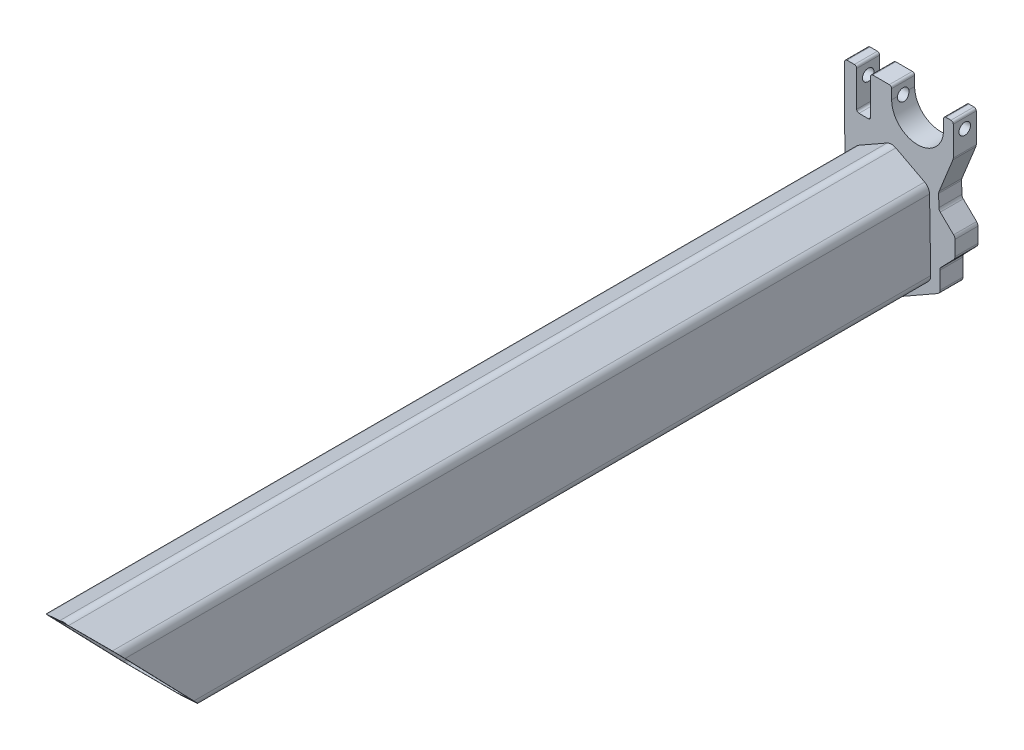
SolidWorks part; units mm, degrees
ref_plane "Front Plane" through (0, 0, 0) normal (0, 0, 1) x (1, 0, 0)
ref_plane "Top Plane" through (0, 0, 0) normal (0, 1, 0) x (1, 0, 0)
ref_plane "Right Plane" through (0, 0, 0) normal (1, 0, 0) x (0, 0, -1)
sketch "Sketch1" plane through (0, 0, 0) normal (0, 0, 1) x (1, 0, 0)
  line L0 (36.798, 101.1427) -> (103.7813, 99.6461) construction
  line L1 (186.6641, 194.1815) -> (187.2024, 162.2454) construction
  line L2 (186.2603, 189.6698) -> (180.1183, 186.1756)
  line L3 (179.6129, 185.2895) -> (179.8695, 170.0721)
  line L4 (180.4044, 169.2036) -> (186.6607, 165.9184)
  line L5 (186.1888, 193.9111) -> (177.0749, 188.7261) construction
  line L6 (176.5695, 187.8401) -> (176.8999, 168.243)
  line L7 (177.4348, 167.3745) -> (186.7183, 162.4997)
  line L8 (193.7621, 169.4288) -> (187.6201, 165.9346)
  line L9 (196.7916, 167.7008) -> (187.6777, 162.5158)
  line L10 (194.0109, 185.5323) -> (194.2674, 170.3148)
  line L11 (196.9666, 188.184) -> (197.297, 168.5868) construction
  line L12 (187.2197, 189.686) -> (193.4759, 186.4008)
  line L13 (187.1482, 193.9273) -> (196.4317, 189.0525) construction
  line L14 (197.297, 168.5868) -> (197.2345, 172.292)
  line L15 (197.5154, 173.004) -> (200.2668, 175.8497)
  line L16 (200.5479, 176.5448) -> (200.5479, 179.7792)
  line L17 (200.2429, 180.4982) -> (197.3418, 183.3031)
  line L18 (197.0371, 184.0052) -> (196.9923, 186.6585)
  line L19 (197.0653, 187.0506) -> (200.0964, 194.5373)
  line L20 (200.1695, 194.9125) -> (200.1695, 201.2852)
  line L21 (199.6695, 201.7852) -> (198.5695, 201.7852)
  line L22 (198.0695, 201.2852) -> (198.0695, 199.1852)
  line L23 (182.6695, 201.7852) -> (186.2695, 201.7852)
  line L24 (186.7695, 201.2852) -> (186.7695, 199.1852)
  line L25 (182.1695, 201.2852) -> (182.1695, 193.5852)
  line L26 (181.6695, 193.0852) -> (179.6695, 193.0852)
  line L27 (179.1695, 193.5852) -> (179.1695, 201.2852)
  line L28 (178.6695, 201.7852) -> (177.0695, 201.7852)
  line L29 (176.5695, 201.2852) -> (176.5695, 187.8401)
  line L30 (176.5695, 201.7852) -> (200.1695, 201.7852) construction
  line L31 (198.0695, 199.1852) -> (186.7695, 199.1852) construction
  arc A0 (177.4348, 167.3745) -> (176.8999, 168.243) centre (177.8997, 168.2598) cw construction
  arc A1 (176.5695, 187.8401) -> (177.0749, 188.7261) centre (177.5694, 187.857) cw construction
  arc A2 (196.9666, 188.184) -> (196.4317, 189.0525) centre (195.9667, 188.1671) ccw construction
  arc A3 (194.2674, 170.3148) -> (193.7621, 169.4288) centre (193.2676, 170.2979) cw
  arc A4 (187.6201, 165.9346) -> (186.6607, 165.9184) centre (187.1256, 166.8037) cw
  arc A5 (180.4044, 169.2036) -> (179.8695, 170.0721) centre (180.8693, 170.0889) cw
  arc A6 (194.0109, 185.5323) -> (193.4759, 186.4008) centre (193.011, 185.5154) ccw
  arc A7 (187.1482, 193.9273) -> (186.1888, 193.9111) centre (186.6833, 193.0419) ccw construction
  arc A8 (187.2197, 189.686) -> (186.2603, 189.6698) centre (186.7548, 188.8006) ccw
  arc A9 (196.7916, 167.7008) -> (197.297, 168.5868) centre (196.2971, 168.57) ccw
  arc A10 (196.4317, 189.0525) -> (196.9666, 188.184) centre (195.9667, 188.1671) cw construction
  arc A11 (176.8999, 168.243) -> (177.4348, 167.3745) centre (177.8997, 168.2598) ccw
  arc A12 (177.0749, 188.7261) -> (176.5695, 187.8401) centre (177.5694, 187.857) ccw construction
  arc A13 (179.6129, 185.2895) -> (180.1183, 186.1756) centre (180.6128, 185.3064) cw
  arc A14 (187.6777, 162.5158) -> (186.7183, 162.4997) centre (187.1832, 163.385) cw
  arc A15 (198.0695, 199.1852) -> (186.7695, 199.1852) centre (192.4195, 199.1852) cw
  arc A16 (200.1695, 194.9125) -> (200.0964, 194.5373) centre (199.1695, 194.9125) cw
  arc A17 (197.0653, 187.0506) -> (196.9923, 186.6585) centre (197.9922, 186.6753) ccw
  arc A18 (197.3418, 183.3031) -> (197.0371, 184.0052) centre (198.0369, 184.022) cw
  arc A19 (200.2429, 180.4982) -> (200.5479, 179.7792) centre (199.5479, 179.7792) cw
  arc A20 (197.5154, 173.004) -> (197.2345, 172.292) centre (198.2344, 172.3089) ccw
  arc A21 (200.2668, 175.8497) -> (200.5479, 176.5448) centre (199.5479, 176.5448) ccw
  arc A22 (176.5695, 201.2852) -> (177.0695, 201.7852) centre (177.0695, 201.2852) cw
  arc A23 (178.6695, 201.7852) -> (179.1695, 201.2852) centre (178.6695, 201.2852) cw
  arc A24 (179.1695, 193.5852) -> (179.6695, 193.0852) centre (179.6695, 193.5852) ccw
  arc A25 (181.6695, 193.0852) -> (182.1695, 193.5852) centre (181.6695, 193.5852) ccw
  arc A26 (182.1695, 201.2852) -> (182.6695, 201.7852) centre (182.6695, 201.2852) cw
  arc A27 (186.2695, 201.7852) -> (186.7695, 201.2852) centre (186.2695, 201.2852) cw
  arc A28 (198.0695, 201.2852) -> (198.5695, 201.7852) centre (198.5695, 201.2852) cw
  arc A29 (200.1695, 201.2852) -> (199.6695, 201.7852) centre (199.6695, 201.2852) ccw
  point P26 (194.2774, 169.722)
  point P29 (187.1448, 165.6642)
  point P32 (179.8795, 169.4792)
  point P35 (194.0009, 186.1251)
  point P41 (186.7356, 189.9402)
  point P47 (179.6029, 185.8824)
  point P65 (187.2001, 162.3852)
  point P73 (196.9889, 186.862)
  point P76 (197.044, 183.591)
  point P81 (197.2275, 172.7062)
  point P89 (179.1695, 201.7852)
  point P96 (182.1695, 201.7852)
  point P99 (186.7695, 201.7852)
  point P102 (198.0695, 201.7852)
  dimension "D9" = 2.1
  dimension "D3" = 1
  dimension "D10" = 11.3
  dimension "D2" = 1
  dimension "D12" = 1
  dimension "D13" = 0.5
  dimension "D1" = 67
  dimension "D4" = 8.7
  dimension "D5" = 2.6
  dimension "D6" = 3
  dimension "D7" = 39.4
  dimension "D8" = 4.6
  dimension "D11" = 2.6
extrude "Boss-Extrude1" add sketch "Sketch1" along normal blind 5 contours L19 A16 L20 A29 L21 A28 L22 A15 L24 A27 L23 A26 L25 A25 L26 A24 L27 A23 L28 A22 L29 L6 A11 L7 A14 L9 A9 L14 A20 L15 A21 L16 A19 L17 A18 L18 A17 | L12 A6 L10 A3 L8 A4 L4 A5 L3 A13 L2 A8
sketch "Sketch2" plane through (0, 0, 5) normal (0, 0, 1) x (1, 0, 0)
  line L0 (185.7658, 190.539) -> (179.6238, 187.0448)
  line L1 (178.6131, 185.2727) -> (178.8696, 170.0552)
  line L2 (179.9395, 168.3182) -> (186.1958, 165.033)
  line L3 (188.1146, 165.0654) -> (194.2565, 168.5596)
  line L4 (195.2673, 170.3317) -> (195.0107, 185.5491)
  line L5 (193.9408, 187.2861) -> (187.6846, 190.5713)
  line L6 (186.2603, 189.6698) -> (180.1183, 186.1756)
  line L7 (193.4759, 186.4008) -> (187.2197, 189.686)
  line L8 (194.2674, 170.3148) -> (194.0109, 185.5323)
  line L9 (187.6201, 165.9346) -> (193.7621, 169.4288)
  line L10 (180.4044, 169.2036) -> (186.6607, 165.9184)
  line L11 (179.6129, 185.2895) -> (179.8695, 170.0721)
  line L12 (186.2603, 189.6698) -> (180.1183, 186.1756)
  line L13 (193.4759, 186.4008) -> (187.2197, 189.686)
  line L14 (194.2674, 170.3148) -> (194.0109, 185.5323)
  line L15 (187.6201, 165.9346) -> (193.7621, 169.4288)
  line L16 (180.4044, 169.2036) -> (186.6607, 165.9184)
  line L17 (179.6129, 185.2895) -> (179.8695, 170.0721)
  arc A0 (179.6238, 187.0448) -> (178.6131, 185.2727) centre (180.6128, 185.3064) ccw
  arc A1 (178.8696, 170.0552) -> (179.9395, 168.3182) centre (180.8693, 170.0889) ccw
  arc A2 (186.1958, 165.033) -> (188.1146, 165.0654) centre (187.1256, 166.8037) ccw
  arc A3 (194.2565, 168.5596) -> (195.2673, 170.3317) centre (193.2676, 170.2979) ccw
  arc A4 (195.0107, 185.5491) -> (193.9408, 187.2861) centre (193.011, 185.5154) ccw
  arc A5 (187.6846, 190.5713) -> (185.7658, 190.539) centre (186.7548, 188.8006) ccw
  arc A6 (187.2197, 189.686) -> (186.2603, 189.6698) centre (186.7548, 188.8006) ccw
  arc A7 (194.0109, 185.5323) -> (193.4759, 186.4008) centre (193.011, 185.5154) ccw
  arc A8 (193.7621, 169.4288) -> (194.2674, 170.3148) centre (193.2676, 170.2979) ccw
  arc A9 (186.6607, 165.9184) -> (187.6201, 165.9346) centre (187.1256, 166.8037) ccw
  arc A10 (179.8695, 170.0721) -> (180.4044, 169.2036) centre (180.8693, 170.0889) ccw
  arc A11 (180.1183, 186.1756) -> (179.6129, 185.2895) centre (180.6128, 185.3064) ccw
  arc A12 (187.2197, 189.686) -> (186.2603, 189.6698) centre (186.7548, 188.8006) ccw
  arc A13 (194.0109, 185.5323) -> (193.4759, 186.4008) centre (193.011, 185.5154) ccw
  arc A14 (193.7621, 169.4288) -> (194.2674, 170.3148) centre (193.2676, 170.2979) ccw
  arc A15 (186.6607, 165.9184) -> (187.6201, 165.9346) centre (187.1256, 166.8037) ccw
  arc A16 (179.8695, 170.0721) -> (180.4044, 169.2036) centre (180.8693, 170.0889) ccw
  arc A17 (180.1183, 186.1756) -> (179.6129, 185.2895) centre (180.6128, 185.3064) ccw
  dimension "D1" = 0
  dimension "D2" = 1
extrude "Boss-Extrude2" add sketch "Sketch2" along normal blind 180
sketch "Sketch3" plane through (181.6848, 3.0629, 0) normal (-0.9999, -0.0169, 0) x (0, 0, 1)
  line L0 (185, 187.5033) -> (185, 161.6259)
  line L1 (185, 187.3807) -> (185, 187.6259) construction
  line L2 (2.5, 198.7719) -> (2.5, 195.7719) construction
  line L3 (185, 161.6259) -> (160, 161.6259)
  line L4 (160, 161.6259) -> (185, 187.5033)
  line L5 (5, 165.2613) -> (5, 161.8711) construction
  line L6 (5, 161.6259) -> (185, 161.6259) construction
  line L7 (5, 198.7719) -> (0, 198.7719) construction
  circle A0 centre (2.5, 195.7719) radius 1.25
  dimension "D2" = 3
  dimension "D3" = 2.5
  dimension "D1" = 155
extrude "Cut-Extrude1" cut sketch "Sketch3" against normal blind 180 and the other way blind 180 contours L4 L0 L3 | A0
ref_plane "Plane3" through (189.8836, 3.2011, 0) normal (-0.9999, -0.0169, 0) x (0, 0, 1)
ref_plane "Plane4" through (-2.9435, 174.6011, 0) normal (-0.0169, 0.9999, 0) x (0.9999, 0.0169, 0)
